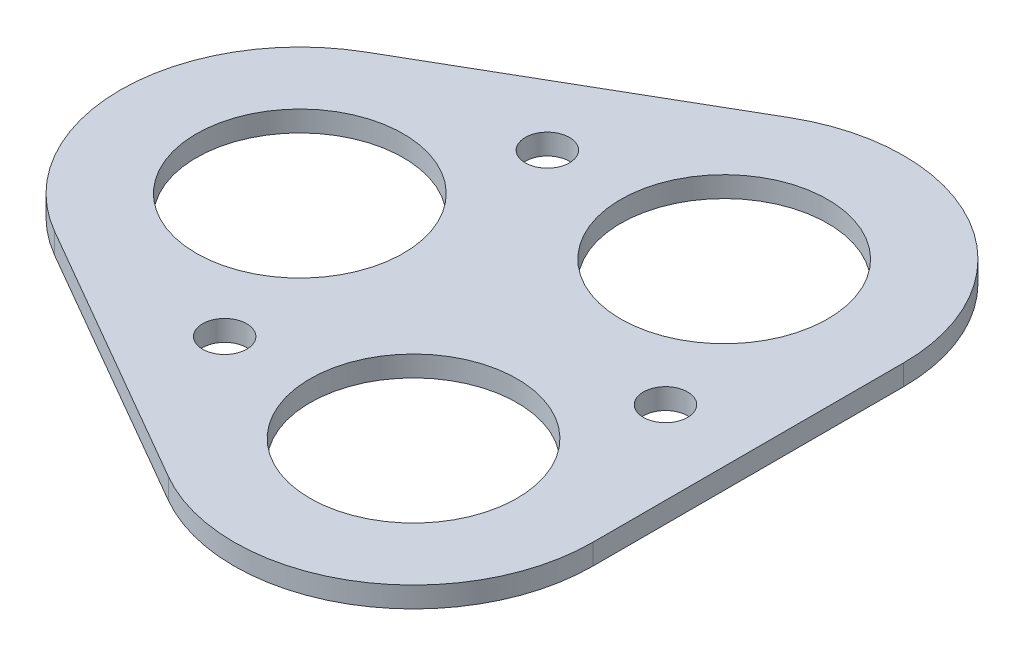
SolidWorks part; units mm, degrees
ref_plane "Front Plane" through (0, 0, 0) normal (0, 0, 1) x (1, 0, 0)
ref_plane "Top Plane" through (0, 0, 0) normal (0, 1, 0) x (1, 0, 0)
ref_plane "Right Plane" through (0, 0, 0) normal (1, 0, 0) x (0, 0, -1)
sketch "Sketch1" plane through (0, 0, 0) normal (0, 1, 0) x (1, 0, 0)
  line L0 (-15.8043, -11.2583) -> (3.6812, -22.5083)
  line L1 (23.1812, -11.25) -> (23.1812, 11.25)
  line L2 (3.6812, 22.5083) -> (-15.8043, 11.2583)
  line L3 (10.1812, -11.25) -> (3.6861, 0) construction
  line L4 (-9.3043, 0) -> (3.6861, 0) construction
  line L5 (10.1812, 11.25) -> (3.6861, 0) construction
  arc A0 (-15.8043, 11.2583) -> (-15.8043, -11.2583) centre (-9.3043, 0) ccw
  arc A1 (3.6812, -22.5083) -> (23.1812, -11.25) centre (10.1812, -11.25) ccw
  arc A2 (23.1812, 11.25) -> (3.6812, 22.5083) centre (10.1812, 11.25) ccw
  circle A3 centre (-9.3043, 0) radius 7.5
  circle A4 centre (-3.0615, 11.6872) radius 1.6
  circle A5 centre (17.1812, 0) radius 1.6
  circle A6 centre (10.1812, -11.25) radius 7.5
  circle A7 centre (10.1812, 11.25) radius 7.5
  circle A8 centre (-3.0615, -11.6872) radius 1.6
  point P21 (3.6861, 0)
  dimension "D1" = 3.2
  dimension "D2" = 15
  dimension "D3" = 19.4856
  dimension "D4" = 22.5
extrude "Boss-Extrude1" add sketch "Sketch1" along normal blind 1.5
